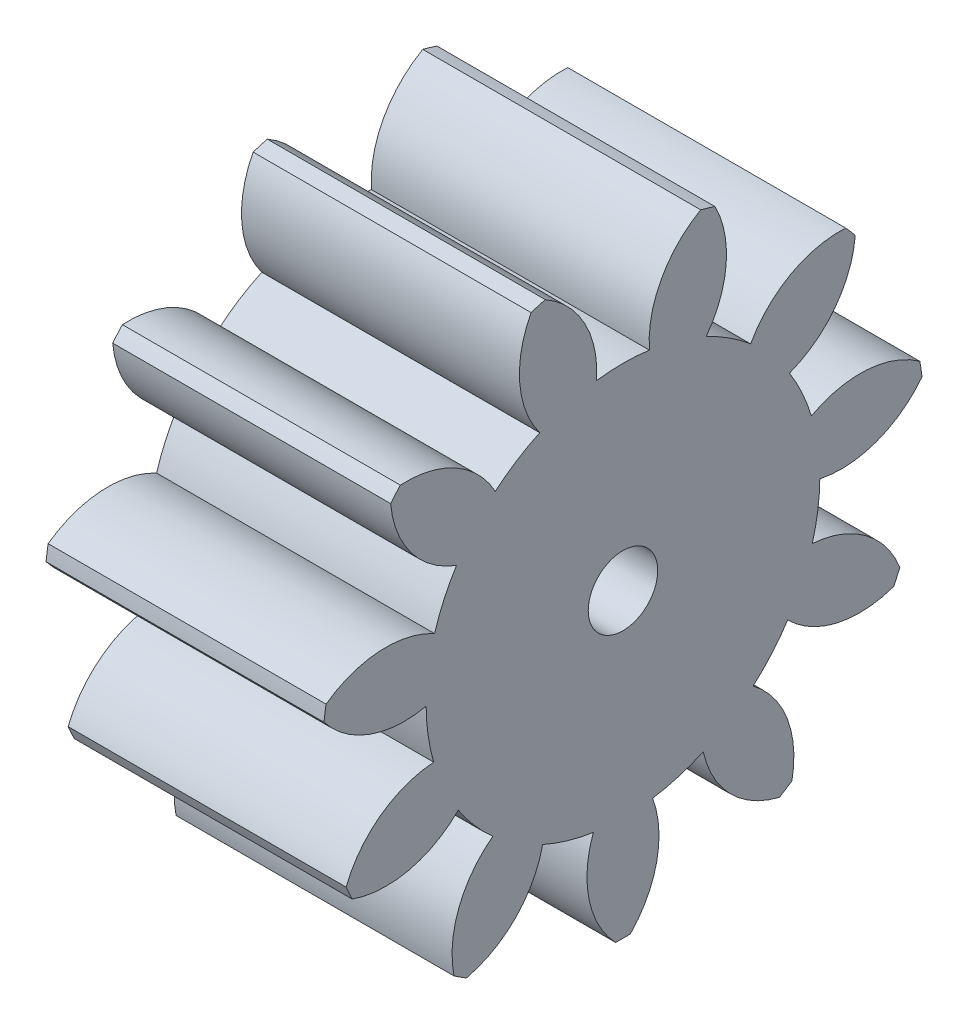
SolidWorks part; units mm, degrees
ref_plane "Plane1" through (0, 0, 0) normal (0, 0, 1) x (1, 0, 0)
ref_plane "Plane2" through (0, 0, 0) normal (0, 1, 0) x (1, 0, 0)
ref_plane "Plane3" through (0, 0, 0) normal (1, 0, 0) x (0, 0, -1)
sketch "HoldingSke" plane through (0, 0, 0) normal (0, 1, 0) x (1, 0, 0)
  line L0 (0, 0) -> (0.4908, -0.0954)
  line L1 (-15, 0) -> (100, 0) construction
  line L2 (0, 0) -> (-2.1039, 2.3779)
  line L3 (0, 0) -> (-11.863, 4.5341)
  line L4 (0, 0) -> (8.4773, 1.6478)
  line L5 (0, 0) -> (-46.8476, -17.4728)
  line L6 (0, 0) -> (-9.9476, -6.7116)
  line L7 (-2.1039, 2.3779) -> (8.6586, 51.2059)
  line L8 (-76.2, 54.61) -> (-75.7, 54.61)
  line L9 (-71.009, 38.7566) -> (-53.1078, 45.2721)
  line L10 (-76.2, 71.12) -> (104.1128, 71.12)
  line L11 (0, 0) -> (-12, 0)
  line L12 (-76.2, 101.6) -> (-76.133, 101.6)
  line L13 (24.9733, 27.94) -> (52.9518, 28.4284)
  line L14 (24.9733, 27.94) -> (24.9743, 27.94)
  line L15 (24.9733, 27.94) -> (100.4006, 29.5858)
  line L16 (-63.627, -2) -> (-12.827, -2)
  circle A0 centre (0, 0) radius 1.5
  circle A1 centre (0, 0) radius 8.499
  circle A2 centre (0, 0) radius 37.5
  circle A3 centre (0, 0) radius 1.5
  dimension "MHD" = 16.998
  dimension "Hub_dia" = 75
  dimension "Bore" = 3
  dimension "MBD" = 3
  dimension "Num_teeth" = 11
  dimension "Pitch" = 0.5
  dimension "Overall_len" = 50
  dimension "Show_teeth" = 11
  dimension "Thickness" = 12
  dimension "OAL" = 50.0001
  dimension "T_dim" = 0.5
  dimension "Ap" = 20
  dimension "H" = 19.05
  dimension "Pitch_radius" = 180.3128
  dimension "Width" = 12
  dimension "Backlash" = 0.067
  dimension "Addendum_fac" = 1
  dimension "Dedendum_fac" = 1.25
  dimension "Clearance_fac" = 0.25
  dimension "Dedendum_add" = 0.001
  dimension "Module" = 2
sketch "BasProSke" plane through (0, 0, 0) normal (0, 1, 0) x (1, 0, 0)
  line L0 (-10, 0) -> (60, 0) construction
  line L1 (0, 0) -> (0, 13)
  line L2 (0, 0) -> (12, 0)
  line L3 (12, 0) -> (12, 13)
  line L4 (12, 13) -> (0, 13)
  dimension "Thickness" = 12
  dimension "Diameter" = 26
revolve "Base-Revolve" add sketch "BasProSke" angle 360 about L0
sketch "TooCutSke" plane through (0, 0, 0) normal (1, 0, 0) x (0, 0, -1)
  line L1 (0, 0) -> (0, 107) construction
  line L2 (0, 0) -> (-1.6825, 10.8706) construction
  line L3 (0, 0) -> (-6.1442, 20.9251) construction
  line L4 (-1.6825, 10.8706) -> (-3.0721, 10.4626) construction
  arc A0 (1.1399, 8.4222) -> (-1.1399, 8.4222) centre (0, 0) ccw
  arc A1 (3.3871, 12.5773) -> (-3.3871, 12.5773) centre (0, 0) ccw
  circle A2 centre (0, 0) radius 11 construction
  circle A3 centre (0, 0) radius 10.3366 construction
  arc A4 (-1.1399, 8.4222) -> (-3.3871, 12.5773) centre (-5.5288, 8.7337) ccw
  arc A5 (3.3871, 12.5773) -> (1.1399, 8.4222) centre (5.5288, 8.7337) ccw
  dimension "Root_dia" = 16.998
  dimension "Overcut_dia" = 26.0508
  dimension "Pitch_dia" = 22
  dimension "Base_dia" = 20.6732
  dimension "Flank_rad" = 4.4
  dimension "Half_ang" = 16.364
  dimension "Half_CT" = 1.4482
extrude "ToothCut" cut sketch "TooCutSke" along normal through all
fillet "Breaks" [suppressed] radius 0.04
fillet "RootFillets" [suppressed] radius 0.501
pattern_circular "TeethCuts" count 11 every 32.727 about axis through (-10, 0, 0) along (1, 0, 0) of "ToothCut", "RootFillets", "Breaks"
sketch "HubNeaOneSke" plane through (0, 0, 0) normal (-1, 0, 0) x (0, 0, 1)
  circle A0 centre (0, 0) radius 8.499
  dimension "Diameter" = 16.998
extrude "HubNearOne" [suppressed] add sketch "HubNeaOneSke" along normal blind 38.0001
sketch "HubNeaBotSke" plane through (0, 0, 0) normal (-1, 0, 0) x (0, 0, 1)
  circle A0 centre (0, 0) radius 8.499
  dimension "Diameter" = 16.998
extrude "HubNearBoth" [suppressed] add sketch "HubNeaBotSke" along normal blind 19
ref_plane "FarPln" through (12, 0, 0) normal (1, 0, 0) x (0, 0, -1)
sketch "HubFarSke" plane through (12, 0, 0) normal (1, 0, 0) x (0, 0, -1)
  circle A0 centre (0, 0) radius 8.499
  dimension "Diameter" = 16.998
extrude "HubFar" [suppressed] add sketch "HubFarSke" along normal blind 19
sketch "BorSke" plane through (0, 0, 0) normal (1, 0, 0) x (0, 0, -1)
  circle A0 centre (0, 0) radius 1.5
  dimension "Diameter" = 3
extrude "Bore" cut sketch "BorSke" along normal mid plane 100.0001
sketch "KeySke" plane through (0, 0, 0) normal (1, 0, 0) x (0, 0, -1)
  line L0 (-0.6, 0) -> (-0.6, 2)
  line L1 (-0.6, 2) -> (0.6, 2)
  line L2 (0.6, 2) -> (0.6, 0)
  line L3 (0, 0) -> (0, 34) construction
  line L4 (-0.6, 0) -> (0.6, 0)
  dimension "Offset" = 2
extrude "Keyway" [suppressed] cut sketch "KeySke" along normal mid plane 100.0001
pattern_circular "Keyway2" [suppressed] count 2 every 90 about axis through (-10, 0, 0) along (1, 0, 0)
equation "' \"Module@HoldingSke\" = 6.35"
equation "' \"Num_teeth@HoldingSke\" = 12"
equation "' \"Ap@HoldingSke\" =  20"
equation "' \"Ap@HoldingSke\" = 20"
equation "' \"Width@HoldingSke\" = 0.5 * 25.4"
equation "' \"Hub_dia@HoldingSke\"= 1 * 25.4"
equation "' \"Hub_dia@HoldingSke\" = 1 * 25.4"
equation "' \"Overall_len@HoldingSke\" = 1.0 * 25.4"
equation "' \"Bore@HoldingSke\" = 0.75 * 25.4"
equation "' \"T_dim@HoldingSke\" = 0.1 * 25.4"
equation "' \"Width@KeySke\" = 0.25 * 25.4"
equation "' \"Show_teeth@HoldingSke\" = 13"
equation "' \"Backlash@HoldingSke\" = 0.009 * 25.4"
equation "' \"Addendum_fac@HoldingSke\" = 1.0"
equation "' \"Dedendum_fac@HoldingSke\" = 1.25"
equation "' \"Dedendum_add@HoldingSke\" = 0.00005 * 25.4"
equation "' \"Clearance_fac@HoldingSke\" = 0.25"
equation "\"Pitch@HoldingSke\" = 1 / \"Module@HoldingSke\""
equation "\"Overcut_dia@TooCutSke\" = (\"Num_teeth@HoldingSke\" + 2 * \"Addendum_fac@HoldingSke\") / \"Pitch@HoldingSke\" + 0.002 * 25.4"
equation "\"Pitch_dia@TooCutSke\" = \"Num_teeth@HoldingSke\" / \"Pitch@HoldingSke\""
equation "\"Base_dia@TooCutSke\" = \"Num_teeth@HoldingSke\" / \"Pitch@HoldingSke\" * cos((\"Ap@HoldingSke\"  * 3.14159265 / 180))"
equation "\"Root_dia@TooCutSke\" = (\"Num_teeth@HoldingSke\" + 2) / \"Pitch@HoldingSke\" - 2 * (\"Addendum_fac@HoldingSke\" + \"Dedendum_fac@HoldingSke\") / \"Pitch@HoldingSke\" - \"Dedendum_add@HoldingSke\" * 2"
equation "\"Half_ang@TooCutSke\" = 180 / \"Num_teeth@HoldingSke\""
equation "\"Half_CT@TooCutSke\" = \"Num_teeth@HoldingSke\" / \"Pitch@HoldingSke\" * sin((3.14159265 / 2 / \"Num_teeth@HoldingSke\")) / 2 - 7 * \"Backlash@HoldingSke\" / 4"
equation "\"Flank_rad@TooCutSke\" = \"Num_teeth@HoldingSke\" / \"Pitch@HoldingSke\" / 5"
equation "\"Radius@RootFillets\" = \"Clearance_fac@HoldingSke\" / \"Pitch@HoldingSke\" + \"Dedendum_add@HoldingSke\""
equation "\"Break_rad@Breaks\" = 0.02 / \"Pitch@HoldingSke\""
equation "\"Thickness@HoldingSke\" = \"Width@HoldingSke\""
equation "\"OAL@HoldingSke\" = \"Thickness@HoldingSke\""
equation "\"MHD@HoldingSke\" = (\"Num_teeth@HoldingSke\" + 2) / \"Pitch@HoldingSke\" - 2 * (\"Addendum_fac@HoldingSke\" + \"Dedendum_fac@HoldingSke\")  / \"Pitch@HoldingSke\" - \"Dedendum_add@HoldingSke\" * 2"
equation "\"MBD@HoldingSke\" = (\"Num_teeth@HoldingSke\" + 2) / \"Pitch@HoldingSke\" - 2 * (\"Addendum_fac@HoldingSke\" + \"Dedendum_fac@HoldingSke\")  / \"Pitch@HoldingSke\" - \"Dedendum_add@HoldingSke\" * 2 - 0.002 * 25.4"
equation "\"MHD@HoldingSke\" = ((sgn( \"MHD@HoldingSke\" - \"Hub_dia@HoldingSke\" )-1)*( \"MHD@HoldingSke\" - \"Hub_dia@HoldingSke\" ))/-2+ \"Hub_dia@HoldingSke\""
equation "\"MBD@HoldingSke\" = ((sgn( \"MBD@HoldingSke\" - \"Bore@HoldingSke\" )-1)*( \"MBD@HoldingSke\" - \"Bore@HoldingSke\" ))/-2+ \"Bore@HoldingSke\""
equation "\"OAL@HoldingSke\" = ((sgn( \"OAL@HoldingSke\" - \"Overall_len@HoldingSke\" )+1)*( \"OAL@HoldingSke\" - \"Overall_len@HoldingSke\" ))/2 + \"Overall_len@HoldingSke\" + 0.000002 * 25.4"
equation "\"Num_teeth@TeethCuts\" = int( \"Show_teeth@HoldingSke\" ) + 1"
equation "\"Num_teeth@TeethCuts\" = ((sgn( \"Num_teeth@TeethCuts\" - \"Num_teeth@HoldingSke\" )-1)*( \"Num_teeth@TeethCuts\" - \"Num_teeth@HoldingSke\" ))/-2+ \"Num_teeth@HoldingSke\""
equation "\"Num_teeth@TeethCuts\" = ((sgn( \"Num_teeth@TeethCuts\" - 2.0)+1)*( \"Num_teeth@TeethCuts\" - 2.0))/2 +2.0"
equation "\"Angle@TeethCuts\" = 360.0 / \"Num_teeth@HoldingSke\""
equation "\"Diameter@BasProSke\" = (\"Num_teeth@HoldingSke\" + 2 * \"Addendum_fac@HoldingSke\") / \"Pitch@HoldingSke\""
equation "\"Thickness@BasProSke\"  = \"Thickness@HoldingSke\""
equation "' \"Fillet_rad@BasProSke\" =  \"Thickness@HoldingSke\" * 0.05"
equation "' \"Fillet_rad@BasProSke\" = \"Thickness@HoldingSke\" * 0.05"
equation "\"MHD@HoldingSke\" = ((sgn( \"MHD@HoldingSke\" - \"Root_dia@TooCutSke\" )-1)*( \"MHD@HoldingSke\" - \"Root_dia@TooCutSke\" ))/-2+ \"Root_dia@TooCutSke\""
equation "\"Diameter@HubNeaOneSke\" = \"MHD@HoldingSke\""
equation "\"Length@HubNearOne\" = \"OAL@HoldingSke\" - \"Thickness@BasProSke\""
equation "\"Diameter@HubNeaBotSke\" = \"MHD@HoldingSke\""
equation "\"Length@HubNearBoth\" = ( \"OAL@HoldingSke\" - \"Thickness@BasProSke\" ) / 2.0"
equation "\"Thickness@FarPln\" = \"Thickness@BasProSke\""
equation "\"Diameter@HubFarSke\" = \"MHD@HoldingSke\""
equation "\"Length@HubFar\" = ( \"OAL@HoldingSke\" - \"Thickness@BasProSke\" ) / 2.0"
equation "\"Diameter@BorSke\" = \"MBD@HoldingSke\""
equation "\"D1@Bore\" = \"OAL@HoldingSke\" * 2.0"
equation "\"D1@Keyway\" = \"OAL@HoldingSke\" * 2.0"
equation "\"Offset@KeySke\" = \"T_dim@HoldingSke\" + \"MBD@HoldingSke\" / 2.0"
